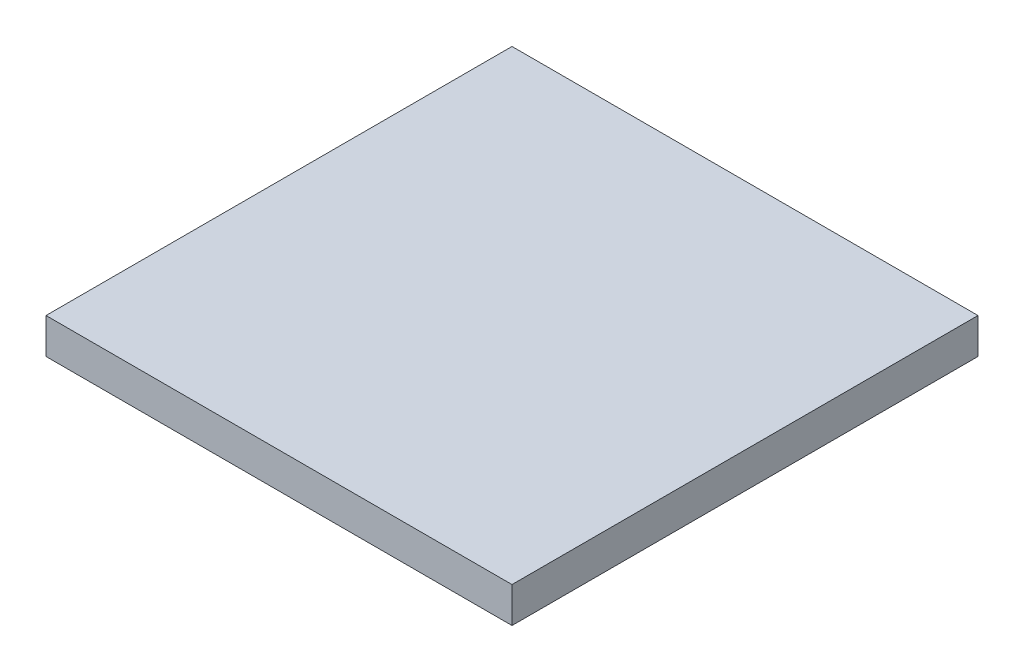
SolidWorks part; units mm, degrees
ref_plane "Front Plane" through (0, 0, 0) normal (0, 0, 1) x (1, 0, 0)
ref_plane "Top Plane" through (0, 0, 0) normal (0, 1, 0) x (1, 0, 0)
ref_plane "Right Plane" through (0, 0, 0) normal (1, 0, 0) x (0, 0, -1)
sketch "Sketch1" plane through (0, 0, 0) normal (0, 1, 0) x (1, 0, 0)
  line L1 (0, 0) -> (5, 0)
  line L2 (0, 0) -> (0, 5)
  line L3 (0, 5) -> (5, 5)
  line L4 (5, 0) -> (5, 5)
  circle A0 centre (2.5, 2.5) radius 1 construction
  point P8 (2.5, 5)
  point P10 (0, 2.5)
  dimension "D3" = 2
  dimension "D1" = 5
  dimension "D2" = 5
extrude "Boss-Extrude1" add sketch "Sketch1" along normal blind 0.381
